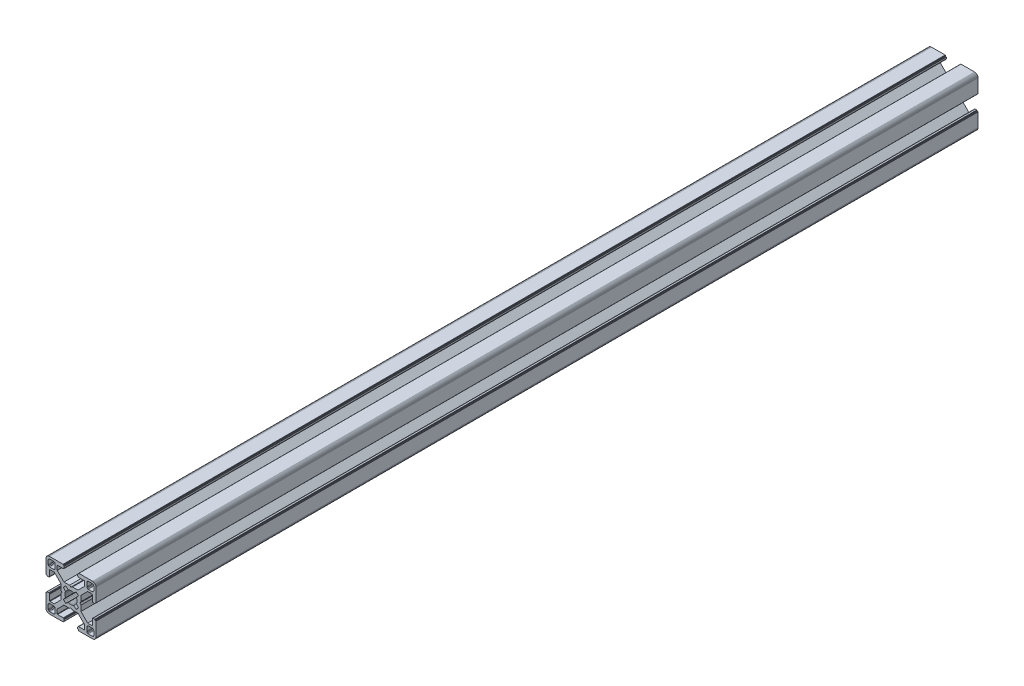
SolidWorks part; units mm, degrees
ref_plane "Front Plane" through (0, 0, 0) normal (0, 0, 1) x (1, 0, 0)
ref_plane "Top Plane" through (0, 0, 0) normal (0, 1, 0) x (1, 0, 0)
ref_plane "Right Plane" through (0, 0, 0) normal (1, 0, 0) x (0, 0, -1)
ref_plane "Plane1" through (0, 0, 0) normal (0, 0, 1) x (1, 0, 0)
sketch "Sketch1" plane through (0, 0, 0) normal (0, 0, 1) x (1, 0, 0)
  line L0 (28.3473, 29.9696) -> (28, 30)
  line L1 (28, 30) -> (19.75, 30)
  line L2 (19.75, 30) -> (19.7153, 29.997)
  line L3 (19.7153, 29.997) -> (19.6816, 29.9879)
  line L4 (19.6816, 29.9879) -> (19.65, 29.9732)
  line L5 (19.65, 29.9732) -> (19.6214, 29.9532)
  line L6 (19.6214, 29.9532) -> (19.5968, 29.9286)
  line L7 (19.5968, 29.9286) -> (19.5768, 29.9)
  line L8 (19.5768, 29.9) -> (19.5621, 29.8684)
  line L9 (19.5621, 29.8684) -> (19.553, 29.8347)
  line L10 (19.553, 29.8347) -> (19.55, 29.8)
  line L11 (19.55, 29.8) -> (19.55, 29.7)
  line L12 (19.55, 29.7) -> (19.547, 29.6653)
  line L13 (19.547, 29.6653) -> (19.5379, 29.6316)
  line L14 (19.5379, 29.6316) -> (19.5232, 29.6)
  line L15 (19.5232, 29.6) -> (19.5032, 29.5714)
  line L16 (19.5032, 29.5714) -> (19.4786, 29.5468)
  line L17 (19.4786, 29.5468) -> (19.45, 29.5268)
  line L18 (19.45, 29.5268) -> (19.4184, 29.5121)
  line L19 (19.4184, 29.5121) -> (19.3847, 29.503)
  line L20 (19.3847, 29.503) -> (19.35, 29.5)
  line L21 (19.35, 29.5) -> (19.25, 29.5)
  line L22 (19.25, 29.5) -> (19.2153, 29.497)
  line L23 (19.2153, 29.497) -> (19.1816, 29.4879)
  line L24 (19.1816, 29.4879) -> (19.15, 29.4732)
  line L25 (19.15, 29.4732) -> (19.1214, 29.4532)
  line L26 (19.1214, 29.4532) -> (19.0968, 29.4286)
  line L27 (19.0968, 29.4286) -> (19.0768, 29.4)
  line L28 (19.0768, 29.4) -> (19.0621, 29.3684)
  line L29 (19.0621, 29.3684) -> (19.053, 29.3347)
  line L30 (19.053, 29.3347) -> (19.05, 29.3)
  line L31 (19.05, 29.3) -> (19.05, 28.4)
  line L32 (19.05, 28.4) -> (19.0591, 28.2958)
  line L33 (19.0591, 28.2958) -> (19.0862, 28.1948)
  line L34 (19.0862, 28.1948) -> (19.1304, 28.1)
  line L35 (19.1304, 28.1) -> (19.1904, 28.0143)
  line L36 (19.1904, 28.0143) -> (19.2643, 27.9404)
  line L37 (19.2643, 27.9404) -> (19.35, 27.8804)
  line L38 (19.35, 27.8804) -> (19.4448, 27.8362)
  line L39 (19.4448, 27.8362) -> (19.5458, 27.8091)
  line L40 (19.5458, 27.8091) -> (19.65, 27.8)
  line L41 (19.65, 27.8) -> (23.05, 27.8)
  line L42 (23.05, 27.8) -> (23.0847, 27.7969)
  line L43 (23.0847, 27.7969) -> (23.1184, 27.7879)
  line L44 (23.1184, 27.7879) -> (23.15, 27.7732)
  line L45 (23.15, 27.7732) -> (23.1786, 27.7532)
  line L46 (23.1786, 27.7532) -> (23.2032, 27.7285)
  line L47 (23.2032, 27.7285) -> (23.2232, 27.7)
  line L48 (23.2232, 27.7) -> (23.2379, 27.6684)
  line L49 (23.2379, 27.6684) -> (23.247, 27.6347)
  line L50 (23.247, 27.6347) -> (23.25, 27.6)
  line L51 (23.25, 27.6) -> (23.25, 25.05)
  line L52 (23.25, 25.05) -> (19.2045, 21)
  line L53 (19.2045, 21) -> (15.9, 21)
  line L54 (15.9, 21) -> (15, 20.4848)
  line L55 (15, 20.4848) -> (14.1, 21)
  line L56 (14.1, 21) -> (10.7955, 21)
  line L57 (10.7955, 21) -> (7.9973, 23.8013)
  line L58 (7.9973, 23.8013) -> (6.75, 25.05)
  line L59 (6.75, 25.05) -> (6.75, 27.6)
  line L60 (6.75, 27.6) -> (6.753, 27.6347)
  line L61 (6.753, 27.6347) -> (6.7621, 27.6684)
  line L62 (6.7621, 27.6684) -> (6.7768, 27.7)
  line L63 (6.7768, 27.7) -> (6.7968, 27.7285)
  line L64 (6.7968, 27.7285) -> (6.8215, 27.7532)
  line L65 (6.8215, 27.7532) -> (6.85, 27.7732)
  line L66 (6.85, 27.7732) -> (6.8816, 27.7879)
  line L67 (6.8816, 27.7879) -> (6.9153, 27.7969)
  line L68 (6.9153, 27.7969) -> (6.95, 27.8)
  line L69 (6.95, 27.8) -> (10.35, 27.8)
  line L70 (10.35, 27.8) -> (10.4542, 27.8091)
  line L71 (10.4542, 27.8091) -> (10.5552, 27.8362)
  line L72 (10.5552, 27.8362) -> (10.65, 27.8804)
  line L73 (10.65, 27.8804) -> (10.7357, 27.9404)
  line L74 (10.7357, 27.9404) -> (10.8096, 28.0143)
  line L75 (10.8096, 28.0143) -> (10.8696, 28.1)
  line L76 (10.8696, 28.1) -> (10.9138, 28.1948)
  line L77 (10.9138, 28.1948) -> (10.9409, 28.2958)
  line L78 (10.9409, 28.2958) -> (10.95, 28.4)
  line L79 (10.95, 28.4) -> (10.95, 29.3)
  line L80 (10.95, 29.3) -> (10.947, 29.3347)
  line L81 (10.947, 29.3347) -> (10.938, 29.3684)
  line L82 (10.938, 29.3684) -> (10.9232, 29.4)
  line L83 (10.9232, 29.4) -> (10.9032, 29.4286)
  line L84 (10.9032, 29.4286) -> (10.8786, 29.4532)
  line L85 (10.8786, 29.4532) -> (10.85, 29.4732)
  line L86 (10.85, 29.4732) -> (10.8184, 29.4879)
  line L87 (10.8184, 29.4879) -> (10.7847, 29.497)
  line L88 (10.7847, 29.497) -> (10.75, 29.5)
  line L89 (10.75, 29.5) -> (10.65, 29.5)
  line L90 (10.65, 29.5) -> (10.6153, 29.503)
  line L91 (10.6153, 29.503) -> (10.5816, 29.5121)
  line L92 (10.5816, 29.5121) -> (10.55, 29.5268)
  line L93 (10.55, 29.5268) -> (10.5214, 29.5468)
  line L94 (10.5214, 29.5468) -> (10.4968, 29.5714)
  line L95 (10.4968, 29.5714) -> (10.4768, 29.6)
  line L96 (10.4768, 29.6) -> (10.4621, 29.6316)
  line L97 (10.4621, 29.6316) -> (10.453, 29.6653)
  line L98 (10.453, 29.6653) -> (10.45, 29.7)
  line L99 (10.45, 29.7) -> (10.45, 29.8)
  line L100 (10.45, 29.8) -> (10.447, 29.8347)
  line L101 (10.447, 29.8347) -> (10.4379, 29.8684)
  line L102 (10.4379, 29.8684) -> (10.4232, 29.9)
  line L103 (10.4232, 29.9) -> (10.4032, 29.9286)
  line L104 (10.4032, 29.9286) -> (10.3786, 29.9532)
  line L105 (10.3786, 29.9532) -> (10.35, 29.9732)
  line L106 (10.35, 29.9732) -> (10.3184, 29.9879)
  line L107 (10.3184, 29.9879) -> (10.2847, 29.997)
  line L108 (10.2847, 29.997) -> (10.25, 30)
  line L109 (10.25, 30) -> (2, 30)
  line L110 (2, 30) -> (1.6527, 29.9696)
  line L111 (1.6527, 29.9696) -> (1.316, 29.8794)
  line L112 (1.316, 29.8794) -> (1, 29.7321)
  line L113 (1, 29.7321) -> (0.7144, 29.5321)
  line L114 (0.7144, 29.5321) -> (0.4679, 29.2856)
  line L115 (0.4679, 29.2856) -> (0.2679, 29)
  line L116 (0.2679, 29) -> (0.1206, 28.684)
  line L117 (0.1206, 28.684) -> (0.0304, 28.3473)
  line L118 (0.0304, 28.3473) -> (0, 28)
  line L119 (0, 28) -> (0, 19.75)
  line L120 (0, 19.75) -> (0.003, 19.7153)
  line L121 (0.003, 19.7153) -> (0.0121, 19.6816)
  line L122 (0.0121, 19.6816) -> (0.0268, 19.65)
  line L123 (0.0268, 19.65) -> (0.0468, 19.6214)
  line L124 (0.0468, 19.6214) -> (0.0714, 19.5968)
  line L125 (0.0714, 19.5968) -> (0.1, 19.5768)
  line L126 (0.1, 19.5768) -> (0.1316, 19.5621)
  line L127 (0.1316, 19.5621) -> (0.1653, 19.553)
  line L128 (0.1653, 19.553) -> (0.2, 19.55)
  line L129 (0.2, 19.55) -> (0.3, 19.55)
  line L130 (0.3, 19.55) -> (0.3347, 19.547)
  line L131 (0.3347, 19.547) -> (0.3684, 19.5379)
  line L132 (0.3684, 19.5379) -> (0.4, 19.5232)
  line L133 (0.4, 19.5232) -> (0.4286, 19.5032)
  line L134 (0.4286, 19.5032) -> (0.4532, 19.4786)
  line L135 (0.4532, 19.4786) -> (0.4732, 19.45)
  line L136 (0.4732, 19.45) -> (0.4879, 19.4184)
  line L137 (0.4879, 19.4184) -> (0.497, 19.3847)
  line L138 (0.497, 19.3847) -> (0.5, 19.35)
  line L139 (0.5, 19.35) -> (0.5, 19.25)
  line L140 (0.5, 19.25) -> (0.503, 19.2153)
  line L141 (0.503, 19.2153) -> (0.5121, 19.1816)
  line L142 (0.5121, 19.1816) -> (0.5268, 19.15)
  line L143 (0.5268, 19.15) -> (0.5468, 19.1214)
  line L144 (0.5468, 19.1214) -> (0.5714, 19.0968)
  line L145 (0.5714, 19.0968) -> (0.6, 19.0768)
  line L146 (0.6, 19.0768) -> (0.6316, 19.0621)
  line L147 (0.6316, 19.0621) -> (0.6653, 19.053)
  line L148 (0.6653, 19.053) -> (0.7, 19.05)
  line L149 (0.7, 19.05) -> (1.6, 19.05)
  line L150 (1.6, 19.05) -> (1.7042, 19.0591)
  line L151 (1.7042, 19.0591) -> (1.8052, 19.0862)
  line L152 (1.8052, 19.0862) -> (1.9, 19.1304)
  line L153 (1.9, 19.1304) -> (1.9857, 19.1904)
  line L154 (1.9857, 19.1904) -> (2.0596, 19.2643)
  line L155 (2.0596, 19.2643) -> (2.1196, 19.35)
  line L156 (2.1196, 19.35) -> (2.1638, 19.4448)
  line L157 (2.1638, 19.4448) -> (2.1909, 19.5458)
  line L158 (2.1909, 19.5458) -> (2.2, 19.65)
  line L159 (2.2, 19.65) -> (2.2, 23.05)
  line L160 (2.2, 23.05) -> (2.203, 23.0847)
  line L161 (2.203, 23.0847) -> (2.2121, 23.1184)
  line L162 (2.2121, 23.1184) -> (2.2268, 23.15)
  line L163 (2.2268, 23.15) -> (2.2468, 23.1786)
  line L164 (2.2468, 23.1786) -> (2.2714, 23.2032)
  line L165 (2.2714, 23.2032) -> (2.3, 23.2232)
  line L166 (2.3, 23.2232) -> (2.3316, 23.2379)
  line L167 (2.3316, 23.2379) -> (2.3653, 23.247)
  line L168 (2.3653, 23.247) -> (2.4, 23.25)
  line L169 (2.4, 23.25) -> (4.95, 23.25)
  line L170 (4.95, 23.25) -> (7.9973, 20.2027)
  line L171 (7.9973, 20.2027) -> (8.9955, 19.2045)
  line L172 (8.9955, 19.2045) -> (8.9955, 15.9)
  line L173 (8.9955, 15.9) -> (9.5151, 15)
  line L174 (9.5151, 15) -> (8.9955, 14.1)
  line L175 (8.9955, 14.1) -> (8.9955, 10.7955)
  line L176 (8.9955, 10.7955) -> (4.95, 6.75)
  line L177 (4.95, 6.75) -> (2.4, 6.75)
  line L178 (2.4, 6.75) -> (2.3653, 6.753)
  line L179 (2.3653, 6.753) -> (2.3316, 6.7621)
  line L180 (2.3316, 6.7621) -> (2.3, 6.7768)
  line L181 (2.3, 6.7768) -> (2.2714, 6.7968)
  line L182 (2.2714, 6.7968) -> (2.2468, 6.8214)
  line L183 (2.2468, 6.8214) -> (2.2268, 6.85)
  line L184 (2.2268, 6.85) -> (2.2121, 6.8816)
  line L185 (2.2121, 6.8816) -> (2.203, 6.9153)
  line L186 (2.203, 6.9153) -> (2.2, 6.95)
  line L187 (2.2, 6.95) -> (2.2, 10.35)
  line L188 (2.2, 10.35) -> (2.1909, 10.4542)
  line L189 (2.1909, 10.4542) -> (2.1638, 10.5552)
  line L190 (2.1638, 10.5552) -> (2.1196, 10.65)
  line L191 (2.1196, 10.65) -> (2.0596, 10.7357)
  line L192 (2.0596, 10.7357) -> (1.9857, 10.8096)
  line L193 (1.9857, 10.8096) -> (1.9, 10.8696)
  line L194 (1.9, 10.8696) -> (1.8052, 10.9138)
  line L195 (1.8052, 10.9138) -> (1.7042, 10.9409)
  line L196 (1.7042, 10.9409) -> (1.6, 10.95)
  line L197 (1.6, 10.95) -> (0.7, 10.95)
  line L198 (0.7, 10.95) -> (0.6653, 10.9469)
  line L199 (0.6653, 10.9469) -> (0.6316, 10.9379)
  line L200 (0.6316, 10.9379) -> (0.6, 10.9232)
  line L201 (0.6, 10.9232) -> (0.5715, 10.9032)
  line L202 (0.5715, 10.9032) -> (0.5468, 10.8785)
  line L203 (0.5468, 10.8785) -> (0.5268, 10.85)
  line L204 (0.5268, 10.85) -> (0.5121, 10.8184)
  line L205 (0.5121, 10.8184) -> (0.503, 10.7847)
  line L206 (0.503, 10.7847) -> (0.5, 10.75)
  line L207 (0.5, 10.75) -> (0.5, 10.65)
  line L208 (0.5, 10.65) -> (0.497, 10.6153)
  line L209 (0.497, 10.6153) -> (0.4879, 10.5816)
  line L210 (0.4879, 10.5816) -> (0.4732, 10.55)
  line L211 (0.4732, 10.55) -> (0.4532, 10.5214)
  line L212 (0.4532, 10.5214) -> (0.4286, 10.4968)
  line L213 (0.4286, 10.4968) -> (0.4, 10.4768)
  line L214 (0.4, 10.4768) -> (0.3684, 10.4621)
  line L215 (0.3684, 10.4621) -> (0.3347, 10.453)
  line L216 (0.3347, 10.453) -> (0.3, 10.45)
  line L217 (0.3, 10.45) -> (0.2, 10.45)
  line L218 (0.2, 10.45) -> (0.1653, 10.447)
  line L219 (0.1653, 10.447) -> (0.1316, 10.4379)
  line L220 (0.1316, 10.4379) -> (0.1, 10.4232)
  line L221 (0.1, 10.4232) -> (0.0714, 10.4032)
  line L222 (0.0714, 10.4032) -> (0.0468, 10.3786)
  line L223 (0.0468, 10.3786) -> (0.0268, 10.35)
  line L224 (0.0268, 10.35) -> (0.0121, 10.3184)
  line L225 (0.0121, 10.3184) -> (0.003, 10.2847)
  line L226 (0.003, 10.2847) -> (0, 10.25)
  line L227 (0, 10.25) -> (0, 2)
  line L228 (0, 2) -> (0.0304, 1.6527)
  line L229 (0.0304, 1.6527) -> (0.1206, 1.316)
  line L230 (0.1206, 1.316) -> (0.2679, 1)
  line L231 (0.2679, 1) -> (0.4679, 0.7144)
  line L232 (0.4679, 0.7144) -> (0.7144, 0.4679)
  line L233 (0.7144, 0.4679) -> (1, 0.2679)
  line L234 (1, 0.2679) -> (1.316, 0.1206)
  line L235 (1.316, 0.1206) -> (1.6527, 0.0304)
  line L236 (1.6527, 0.0304) -> (2, 0)
  line L237 (2, 0) -> (10.25, 0)
  line L238 (10.25, 0) -> (10.2847, 0.003)
  line L239 (10.2847, 0.003) -> (10.3184, 0.0121)
  line L240 (10.3184, 0.0121) -> (10.35, 0.0268)
  line L241 (10.35, 0.0268) -> (10.3786, 0.0468)
  line L242 (10.3786, 0.0468) -> (10.4032, 0.0714)
  line L243 (10.4032, 0.0714) -> (10.4232, 0.1)
  line L244 (10.4232, 0.1) -> (10.4379, 0.1316)
  line L245 (10.4379, 0.1316) -> (10.447, 0.1653)
  line L246 (10.447, 0.1653) -> (10.45, 0.2)
  line L247 (10.45, 0.2) -> (10.45, 0.3)
  line L248 (10.45, 0.3) -> (10.453, 0.3347)
  line L249 (10.453, 0.3347) -> (10.4621, 0.3684)
  line L250 (10.4621, 0.3684) -> (10.4768, 0.4)
  line L251 (10.4768, 0.4) -> (10.4968, 0.4286)
  line L252 (10.4968, 0.4286) -> (10.5214, 0.4532)
  line L253 (10.5214, 0.4532) -> (10.55, 0.4732)
  line L254 (10.55, 0.4732) -> (10.5816, 0.4879)
  line L255 (10.5816, 0.4879) -> (10.6153, 0.497)
  line L256 (10.6153, 0.497) -> (10.65, 0.5)
  line L257 (10.65, 0.5) -> (10.75, 0.5)
  line L258 (10.75, 0.5) -> (10.7847, 0.503)
  line L259 (10.7847, 0.503) -> (10.8184, 0.5121)
  line L260 (10.8184, 0.5121) -> (10.85, 0.5268)
  line L261 (10.85, 0.5268) -> (10.8785, 0.5468)
  line L262 (10.8785, 0.5468) -> (10.9032, 0.5715)
  line L263 (10.9032, 0.5715) -> (10.9232, 0.6)
  line L264 (10.9232, 0.6) -> (10.9379, 0.6316)
  line L265 (10.9379, 0.6316) -> (10.9469, 0.6653)
  line L266 (10.9469, 0.6653) -> (10.95, 0.7)
  line L267 (10.95, 0.7) -> (10.95, 1.6)
  line L268 (10.95, 1.6) -> (10.9409, 1.7042)
  line L269 (10.9409, 1.7042) -> (10.9138, 1.8052)
  line L270 (10.9138, 1.8052) -> (10.8696, 1.9)
  line L271 (10.8696, 1.9) -> (10.8096, 1.9857)
  line L272 (10.8096, 1.9857) -> (10.7357, 2.0596)
  line L273 (10.7357, 2.0596) -> (10.65, 2.1196)
  line L274 (10.65, 2.1196) -> (10.5552, 2.1638)
  line L275 (10.5552, 2.1638) -> (10.4542, 2.1909)
  line L276 (10.4542, 2.1909) -> (10.35, 2.2)
  line L277 (10.35, 2.2) -> (6.95, 2.2)
  line L278 (6.95, 2.2) -> (6.9153, 2.203)
  line L279 (6.9153, 2.203) -> (6.8816, 2.212)
  line L280 (6.8816, 2.212) -> (6.85, 2.2268)
  line L281 (6.85, 2.2268) -> (6.8215, 2.2468)
  line L282 (6.8215, 2.2468) -> (6.7968, 2.2714)
  line L283 (6.7968, 2.2714) -> (6.7768, 2.3)
  line L284 (6.7768, 2.3) -> (6.7621, 2.3316)
  line L285 (6.7621, 2.3316) -> (6.753, 2.3653)
  line L286 (6.753, 2.3653) -> (6.75, 2.4)
  line L287 (6.75, 2.4) -> (6.75, 4.95)
  line L288 (6.75, 4.95) -> (9.7875, 7.9908)
  line L289 (9.7875, 7.9908) -> (10.7955, 9)
  line L290 (10.7955, 9) -> (14.1, 9)
  line L291 (14.1, 9) -> (15, 9.5151)
  line L292 (15, 9.5151) -> (15.9, 9)
  line L293 (15.9, 9) -> (19.2045, 9)
  line L294 (19.2045, 9) -> (20.2126, 7.9908)
  line L295 (20.2126, 7.9908) -> (23.25, 4.95)
  line L296 (23.25, 4.95) -> (23.25, 2.4)
  line L297 (23.25, 2.4) -> (23.247, 2.3653)
  line L298 (23.247, 2.3653) -> (23.2379, 2.3316)
  line L299 (23.2379, 2.3316) -> (23.2232, 2.3)
  line L300 (23.2232, 2.3) -> (23.2032, 2.2714)
  line L301 (23.2032, 2.2714) -> (23.1786, 2.2468)
  line L302 (23.1786, 2.2468) -> (23.15, 2.2268)
  line L303 (23.15, 2.2268) -> (23.1184, 2.212)
  line L304 (23.1184, 2.212) -> (23.0847, 2.203)
  line L305 (23.0847, 2.203) -> (23.05, 2.2)
  line L306 (23.05, 2.2) -> (19.65, 2.2)
  line L307 (19.65, 2.2) -> (19.5458, 2.1909)
  line L308 (19.5458, 2.1909) -> (19.4448, 2.1638)
  line L309 (19.4448, 2.1638) -> (19.35, 2.1196)
  line L310 (19.35, 2.1196) -> (19.2643, 2.0596)
  line L311 (19.2643, 2.0596) -> (19.1904, 1.9857)
  line L312 (19.1904, 1.9857) -> (19.1304, 1.9)
  line L313 (19.1304, 1.9) -> (19.0862, 1.8052)
  line L314 (19.0862, 1.8052) -> (19.0591, 1.7042)
  line L315 (19.0591, 1.7042) -> (19.05, 1.6)
  line L316 (19.05, 1.6) -> (19.05, 0.7)
  line L317 (19.05, 0.7) -> (19.053, 0.6653)
  line L318 (19.053, 0.6653) -> (19.0621, 0.6316)
  line L319 (19.0621, 0.6316) -> (19.0768, 0.6)
  line L320 (19.0768, 0.6) -> (19.0968, 0.5714)
  line L321 (19.0968, 0.5714) -> (19.1214, 0.5468)
  line L322 (19.1214, 0.5468) -> (19.15, 0.5268)
  line L323 (19.15, 0.5268) -> (19.1816, 0.5121)
  line L324 (19.1816, 0.5121) -> (19.2153, 0.503)
  line L325 (19.2153, 0.503) -> (19.25, 0.5)
  line L326 (19.25, 0.5) -> (19.35, 0.5)
  line L327 (19.35, 0.5) -> (19.3847, 0.497)
  line L328 (19.3847, 0.497) -> (19.4184, 0.4879)
  line L329 (19.4184, 0.4879) -> (19.45, 0.4732)
  line L330 (19.45, 0.4732) -> (19.4786, 0.4532)
  line L331 (19.4786, 0.4532) -> (19.5032, 0.4286)
  line L332 (19.5032, 0.4286) -> (19.5232, 0.4)
  line L333 (19.5232, 0.4) -> (19.5379, 0.3684)
  line L334 (19.5379, 0.3684) -> (19.547, 0.3347)
  line L335 (19.547, 0.3347) -> (19.55, 0.3)
  line L336 (19.55, 0.3) -> (19.55, 0.2)
  line L337 (19.55, 0.2) -> (19.553, 0.1653)
  line L338 (19.553, 0.1653) -> (19.5621, 0.1316)
  line L339 (19.5621, 0.1316) -> (19.5768, 0.1)
  line L340 (19.5768, 0.1) -> (19.5968, 0.0714)
  line L341 (19.5968, 0.0714) -> (19.6214, 0.0468)
  line L342 (19.6214, 0.0468) -> (19.65, 0.0268)
  line L343 (19.65, 0.0268) -> (19.6816, 0.0121)
  line L344 (19.6816, 0.0121) -> (19.7153, 0.003)
  line L345 (19.7153, 0.003) -> (19.75, 0)
  line L346 (19.75, 0) -> (28, 0)
  line L347 (28, 0) -> (28.3473, 0.0304)
  line L348 (28.3473, 0.0304) -> (28.684, 0.1206)
  line L349 (28.684, 0.1206) -> (29, 0.2679)
  line L350 (29, 0.2679) -> (29.2856, 0.4679)
  line L351 (29.2856, 0.4679) -> (29.5321, 0.7144)
  line L352 (29.5321, 0.7144) -> (29.7321, 1)
  line L353 (29.7321, 1) -> (29.8794, 1.316)
  line L354 (29.8794, 1.316) -> (29.9696, 1.6527)
  line L355 (29.9696, 1.6527) -> (30, 2)
  line L356 (30, 2) -> (30, 10.25)
  line L357 (30, 10.25) -> (29.997, 10.2847)
  line L358 (29.997, 10.2847) -> (29.988, 10.3184)
  line L359 (29.988, 10.3184) -> (29.9732, 10.35)
  line L360 (29.9732, 10.35) -> (29.9532, 10.3785)
  line L361 (29.9532, 10.3785) -> (29.9286, 10.4032)
  line L362 (29.9286, 10.4032) -> (29.9, 10.4232)
  line L363 (29.9, 10.4232) -> (29.8684, 10.4379)
  line L364 (29.8684, 10.4379) -> (29.8347, 10.447)
  line L365 (29.8347, 10.447) -> (29.8, 10.45)
  line L366 (29.8, 10.45) -> (29.7, 10.45)
  line L367 (29.7, 10.45) -> (29.6649, 10.4534)
  line L368 (29.6649, 10.4534) -> (29.6312, 10.4624)
  line L369 (29.6312, 10.4624) -> (29.5996, 10.4772)
  line L370 (29.5996, 10.4772) -> (29.5711, 10.4972)
  line L371 (29.5711, 10.4972) -> (29.5464, 10.5218)
  line L372 (29.5464, 10.5218) -> (29.5264, 10.5504)
  line L373 (29.5264, 10.5504) -> (29.5117, 10.582)
  line L374 (29.5117, 10.582) -> (29.5027, 10.6156)
  line L375 (29.5027, 10.6156) -> (29.4996, 10.6504)
  line L376 (29.4996, 10.6504) -> (29.4996, 10.7504)
  line L377 (29.4996, 10.7504) -> (29.497, 10.7847)
  line L378 (29.497, 10.7847) -> (29.4879, 10.8184)
  line L379 (29.4879, 10.8184) -> (29.4732, 10.85)
  line L380 (29.4732, 10.85) -> (29.4532, 10.8785)
  line L381 (29.4532, 10.8785) -> (29.4286, 10.9032)
  line L382 (29.4286, 10.9032) -> (29.4, 10.9232)
  line L383 (29.4, 10.9232) -> (29.3684, 10.9379)
  line L384 (29.3684, 10.9379) -> (29.3347, 10.9469)
  line L385 (29.3347, 10.9469) -> (29.3, 10.95)
  line L386 (29.3, 10.95) -> (28.4, 10.95)
  line L387 (28.4, 10.95) -> (28.2958, 10.9409)
  line L388 (28.2958, 10.9409) -> (28.1948, 10.9138)
  line L389 (28.1948, 10.9138) -> (28.1, 10.8696)
  line L390 (28.1, 10.8696) -> (28.0143, 10.8096)
  line L391 (28.0143, 10.8096) -> (27.9404, 10.7357)
  line L392 (27.9404, 10.7357) -> (27.8804, 10.65)
  line L393 (27.8804, 10.65) -> (27.8362, 10.5552)
  line L394 (27.8362, 10.5552) -> (27.8091, 10.4542)
  line L395 (27.8091, 10.4542) -> (27.8, 10.35)
  line L396 (27.8, 10.35) -> (27.8, 6.95)
  line L397 (27.8, 6.95) -> (27.797, 6.9153)
  line L398 (27.797, 6.9153) -> (27.7879, 6.8816)
  line L399 (27.7879, 6.8816) -> (27.7732, 6.85)
  line L400 (27.7732, 6.85) -> (27.7532, 6.8214)
  line L401 (27.7532, 6.8214) -> (27.7286, 6.7968)
  line L402 (27.7286, 6.7968) -> (27.7, 6.7768)
  line L403 (27.7, 6.7768) -> (27.6684, 6.7621)
  line L404 (27.6684, 6.7621) -> (27.6347, 6.753)
  line L405 (27.6347, 6.753) -> (27.6, 6.75)
  line L406 (27.6, 6.75) -> (25.05, 6.75)
  line L407 (25.05, 6.75) -> (23.8092, 7.9908)
  line L408 (23.8092, 7.9908) -> (21.0045, 10.7955)
  line L409 (21.0045, 10.7955) -> (21.0045, 14.1)
  line L410 (21.0045, 14.1) -> (20.4849, 15)
  line L411 (20.4849, 15) -> (21.0045, 15.9)
  line L412 (21.0045, 15.9) -> (21.0045, 19.2045)
  line L413 (21.0045, 19.2045) -> (25.05, 23.25)
  line L414 (25.05, 23.25) -> (27.6, 23.25)
  line L415 (27.6, 23.25) -> (27.6347, 23.247)
  line L416 (27.6347, 23.247) -> (27.6684, 23.2379)
  line L417 (27.6684, 23.2379) -> (27.7, 23.2232)
  line L418 (27.7, 23.2232) -> (27.7286, 23.2032)
  line L419 (27.7286, 23.2032) -> (27.7532, 23.1786)
  line L420 (27.7532, 23.1786) -> (27.7732, 23.15)
  line L421 (27.7732, 23.15) -> (27.7879, 23.1184)
  line L422 (27.7879, 23.1184) -> (27.797, 23.0847)
  line L423 (27.797, 23.0847) -> (27.8, 23.05)
  line L424 (27.8, 23.05) -> (27.8, 19.65)
  line L425 (27.8, 19.65) -> (27.8091, 19.5458)
  line L426 (27.8091, 19.5458) -> (27.8362, 19.4448)
  line L427 (27.8362, 19.4448) -> (27.8804, 19.35)
  line L428 (27.8804, 19.35) -> (27.9404, 19.2643)
  line L429 (27.9404, 19.2643) -> (28.0143, 19.1904)
  line L430 (28.0143, 19.1904) -> (28.1, 19.1304)
  line L431 (28.1, 19.1304) -> (28.1948, 19.0862)
  line L432 (28.1948, 19.0862) -> (28.2958, 19.0591)
  line L433 (28.2958, 19.0591) -> (28.4, 19.05)
  line L434 (28.4, 19.05) -> (29.3, 19.05)
  line L435 (29.3, 19.05) -> (29.3347, 19.053)
  line L436 (29.3347, 19.053) -> (29.3684, 19.0621)
  line L437 (29.3684, 19.0621) -> (29.4, 19.0768)
  line L438 (29.4, 19.0768) -> (29.4282, 19.0971)
  line L439 (29.4282, 19.0971) -> (29.4528, 19.1218)
  line L440 (29.4528, 19.1218) -> (29.4728, 19.1504)
  line L441 (29.4728, 19.1504) -> (29.4876, 19.182)
  line L442 (29.4876, 19.182) -> (29.4966, 19.2156)
  line L443 (29.4966, 19.2156) -> (29.4996, 19.2504)
  line L444 (29.4996, 19.2504) -> (29.4996, 19.3504)
  line L445 (29.4996, 19.3504) -> (29.5027, 19.3851)
  line L446 (29.5027, 19.3851) -> (29.5117, 19.4188)
  line L447 (29.5117, 19.4188) -> (29.5264, 19.4504)
  line L448 (29.5264, 19.4504) -> (29.5464, 19.4789)
  line L449 (29.5464, 19.4789) -> (29.5711, 19.5036)
  line L450 (29.5711, 19.5036) -> (29.5996, 19.5236)
  line L451 (29.5996, 19.5236) -> (29.6312, 19.5383)
  line L452 (29.6312, 19.5383) -> (29.6649, 19.5473)
  line L453 (29.6649, 19.5473) -> (29.7, 19.55)
  line L454 (29.7, 19.55) -> (29.8, 19.55)
  line L455 (29.8, 19.55) -> (29.8347, 19.553)
  line L456 (29.8347, 19.553) -> (29.8684, 19.5621)
  line L457 (29.8684, 19.5621) -> (29.9, 19.5768)
  line L458 (29.9, 19.5768) -> (29.9286, 19.5968)
  line L459 (29.9286, 19.5968) -> (29.9532, 19.6214)
  line L460 (29.9532, 19.6214) -> (29.9732, 19.65)
  line L461 (29.9732, 19.65) -> (29.9879, 19.6816)
  line L462 (29.9879, 19.6816) -> (29.997, 19.7153)
  line L463 (29.997, 19.7153) -> (30, 19.75)
  line L464 (30, 19.75) -> (30, 28)
  line L465 (30, 28) -> (29.9696, 28.3473)
  line L466 (29.9696, 28.3473) -> (29.8794, 28.684)
  line L467 (29.8794, 28.684) -> (29.7321, 29)
  line L468 (29.7321, 29) -> (29.5321, 29.2856)
  line L469 (29.5321, 29.2856) -> (29.2856, 29.5321)
  line L470 (29.2856, 29.5321) -> (29, 29.7321)
  line L471 (29, 29.7321) -> (28.684, 29.8794)
  line L472 (28.684, 29.8794) -> (28.3473, 29.9696)
  line L473 (1.3, 25.5) -> (1.3, 27.7)
  line L474 (1.3, 27.7) -> (1.3123, 27.8564)
  line L475 (1.3123, 27.8564) -> (1.3489, 28.009)
  line L476 (1.3489, 28.009) -> (1.409, 28.154)
  line L477 (1.409, 28.154) -> (1.491, 28.2878)
  line L478 (1.491, 28.2878) -> (1.5929, 28.4071)
  line L479 (1.5929, 28.4071) -> (1.7122, 28.509)
  line L480 (1.7122, 28.509) -> (1.846, 28.591)
  line L481 (1.846, 28.591) -> (1.991, 28.6511)
  line L482 (1.991, 28.6511) -> (2.1436, 28.6877)
  line L483 (2.1436, 28.6877) -> (2.3, 28.7)
  line L484 (2.3, 28.7) -> (4.5, 28.7)
  line L485 (4.5, 28.7) -> (4.6564, 28.6877)
  line L486 (4.6564, 28.6877) -> (4.809, 28.6511)
  line L487 (4.809, 28.6511) -> (4.954, 28.591)
  line L488 (4.954, 28.591) -> (5.0878, 28.509)
  line L489 (5.0878, 28.509) -> (5.2071, 28.4071)
  line L490 (5.2071, 28.4071) -> (5.309, 28.2878)
  line L491 (5.309, 28.2878) -> (5.391, 28.154)
  line L492 (5.391, 28.154) -> (5.4511, 28.009)
  line L493 (5.4511, 28.009) -> (5.4877, 27.8564)
  line L494 (5.4877, 27.8564) -> (5.5, 27.7)
  line L495 (5.5, 27.7) -> (5.5, 25.5)
  line L496 (5.5, 25.5) -> (5.4877, 25.3436)
  line L497 (5.4877, 25.3436) -> (5.4511, 25.191)
  line L498 (5.4511, 25.191) -> (5.391, 25.046)
  line L499 (5.391, 25.046) -> (5.309, 24.9122)
  line L500 (5.309, 24.9122) -> (5.2071, 24.7929)
  line L501 (5.2071, 24.7929) -> (5.0878, 24.691)
  line L502 (5.0878, 24.691) -> (4.954, 24.609)
  line L503 (4.954, 24.609) -> (4.809, 24.5489)
  line L504 (4.809, 24.5489) -> (4.6564, 24.5123)
  line L505 (4.6564, 24.5123) -> (4.5, 24.5)
  line L506 (4.5, 24.5) -> (2.3, 24.5)
  line L507 (2.3, 24.5) -> (2.1436, 24.5123)
  line L508 (2.1436, 24.5123) -> (1.991, 24.5489)
  line L509 (1.991, 24.5489) -> (1.846, 24.609)
  line L510 (1.846, 24.609) -> (1.7122, 24.691)
  line L511 (1.7122, 24.691) -> (1.5929, 24.7929)
  line L512 (1.5929, 24.7929) -> (1.491, 24.9122)
  line L513 (1.491, 24.9122) -> (1.409, 25.046)
  line L514 (1.409, 25.046) -> (1.3489, 25.191)
  line L515 (1.3489, 25.191) -> (1.3123, 25.3436)
  line L516 (1.3123, 25.3436) -> (1.3, 25.5)
  line L517 (25.3436, 28.6877) -> (25.5, 28.7)
  line L518 (25.5, 28.7) -> (27.7, 28.7)
  line L519 (27.7, 28.7) -> (27.8564, 28.6877)
  line L520 (27.8564, 28.6877) -> (28.009, 28.6511)
  line L521 (28.009, 28.6511) -> (28.154, 28.591)
  line L522 (28.154, 28.591) -> (28.2878, 28.509)
  line L523 (28.2878, 28.509) -> (28.4071, 28.4071)
  line L524 (28.4071, 28.4071) -> (28.509, 28.2878)
  line L525 (28.509, 28.2878) -> (28.591, 28.154)
  line L526 (28.591, 28.154) -> (28.6511, 28.009)
  line L527 (28.6511, 28.009) -> (28.6877, 27.8564)
  line L528 (28.6877, 27.8564) -> (28.7, 27.7)
  line L529 (28.7, 27.7) -> (28.7, 25.5)
  line L530 (28.7, 25.5) -> (28.6877, 25.3436)
  line L531 (28.6877, 25.3436) -> (28.6511, 25.191)
  line L532 (28.6511, 25.191) -> (28.591, 25.046)
  line L533 (28.591, 25.046) -> (28.509, 24.9122)
  line L534 (28.509, 24.9122) -> (28.4071, 24.7929)
  line L535 (28.4071, 24.7929) -> (28.2878, 24.691)
  line L536 (28.2878, 24.691) -> (28.154, 24.609)
  line L537 (28.154, 24.609) -> (28.009, 24.5489)
  line L538 (28.009, 24.5489) -> (27.8564, 24.5123)
  line L539 (27.8564, 24.5123) -> (27.7, 24.5)
  line L540 (27.7, 24.5) -> (25.5, 24.5)
  line L541 (25.5, 24.5) -> (25.3436, 24.5123)
  line L542 (25.3436, 24.5123) -> (25.191, 24.5489)
  line L543 (25.191, 24.5489) -> (25.046, 24.609)
  line L544 (25.046, 24.609) -> (24.9122, 24.691)
  line L545 (24.9122, 24.691) -> (24.7929, 24.7929)
  line L546 (24.7929, 24.7929) -> (24.691, 24.9122)
  line L547 (24.691, 24.9122) -> (24.609, 25.046)
  line L548 (24.609, 25.046) -> (24.5489, 25.191)
  line L549 (24.5489, 25.191) -> (24.5123, 25.3436)
  line L550 (24.5123, 25.3436) -> (24.5, 25.5)
  line L551 (24.5, 25.5) -> (24.5, 27.7)
  line L552 (24.5, 27.7) -> (24.5123, 27.8564)
  line L553 (24.5123, 27.8564) -> (24.5489, 28.009)
  line L554 (24.5489, 28.009) -> (24.609, 28.154)
  line L555 (24.609, 28.154) -> (24.691, 28.2878)
  line L556 (24.691, 28.2878) -> (24.7929, 28.4071)
  line L557 (24.7929, 28.4071) -> (24.9122, 28.509)
  line L558 (24.9122, 28.509) -> (25.046, 28.591)
  line L559 (25.046, 28.591) -> (25.191, 28.6511)
  line L560 (25.191, 28.6511) -> (25.3436, 28.6877)
  line L561 (15, 18.65) -> (15.55, 18.6083)
  line L562 (15.55, 18.6083) -> (16.0875, 18.4842)
  line L563 (16.0875, 18.4842) -> (16.6001, 18.2806)
  line L564 (16.6001, 18.2806) -> (18.1359, 19.5184)
  line L565 (18.1359, 19.5184) -> (18.645, 19.1187)
  line L566 (18.645, 19.1187) -> (19.1036, 18.6621)
  line L567 (19.1036, 18.6621) -> (19.5053, 18.1547)
  line L568 (19.5053, 18.1547) -> (18.2806, 16.6001)
  line L569 (18.2806, 16.6001) -> (18.4842, 16.0875)
  line L570 (18.4842, 16.0875) -> (18.6083, 15.55)
  line L571 (18.6083, 15.55) -> (18.65, 15)
  line L572 (18.65, 15) -> (18.6083, 14.45)
  line L573 (18.6083, 14.45) -> (18.4842, 13.9125)
  line L574 (18.4842, 13.9125) -> (18.2806, 13.3999)
  line L575 (18.2806, 13.3999) -> (19.5053, 11.8453)
  line L576 (19.5053, 11.8453) -> (19.1036, 11.3379)
  line L577 (19.1036, 11.3379) -> (18.645, 10.8813)
  line L578 (18.645, 10.8813) -> (18.1359, 10.4816)
  line L579 (18.1359, 10.4816) -> (16.6001, 11.7194)
  line L580 (16.6001, 11.7194) -> (16.0875, 11.5158)
  line L581 (16.0875, 11.5158) -> (15.55, 11.3917)
  line L582 (15.55, 11.3917) -> (15, 11.35)
  line L583 (15, 11.35) -> (14.45, 11.3917)
  line L584 (14.45, 11.3917) -> (13.9125, 11.5158)
  line L585 (13.9125, 11.5158) -> (13.3999, 11.7194)
  line L586 (13.3999, 11.7194) -> (11.8641, 10.4816)
  line L587 (11.8641, 10.4816) -> (11.355, 10.8813)
  line L588 (11.355, 10.8813) -> (10.8964, 11.3379)
  line L589 (10.8964, 11.3379) -> (10.4947, 11.8453)
  line L590 (10.4947, 11.8453) -> (11.7194, 13.3999)
  line L591 (11.7194, 13.3999) -> (11.5158, 13.9125)
  line L592 (11.5158, 13.9125) -> (11.3917, 14.45)
  line L593 (11.3917, 14.45) -> (11.35, 15)
  line L594 (11.35, 15) -> (11.3917, 15.55)
  line L595 (11.3917, 15.55) -> (11.5158, 16.0875)
  line L596 (11.5158, 16.0875) -> (11.7194, 16.6001)
  line L597 (11.7194, 16.6001) -> (10.4947, 18.1547)
  line L598 (10.4947, 18.1547) -> (10.8964, 18.6621)
  line L599 (10.8964, 18.6621) -> (11.355, 19.1187)
  line L600 (11.355, 19.1187) -> (11.8641, 19.5184)
  line L601 (11.8641, 19.5184) -> (13.3999, 18.2806)
  line L602 (13.3999, 18.2806) -> (13.9125, 18.4842)
  line L603 (13.9125, 18.4842) -> (14.45, 18.6083)
  line L604 (14.45, 18.6083) -> (15, 18.65)
  line L605 (4.5, 1.3) -> (2.3, 1.3)
  line L606 (2.3, 1.3) -> (2.1436, 1.3123)
  line L607 (2.1436, 1.3123) -> (1.991, 1.3489)
  line L608 (1.991, 1.3489) -> (1.846, 1.409)
  line L609 (1.846, 1.409) -> (1.7122, 1.491)
  line L610 (1.7122, 1.491) -> (1.5929, 1.5929)
  line L611 (1.5929, 1.5929) -> (1.491, 1.7122)
  line L612 (1.491, 1.7122) -> (1.409, 1.846)
  line L613 (1.409, 1.846) -> (1.3489, 1.991)
  line L614 (1.3489, 1.991) -> (1.3123, 2.1436)
  line L615 (1.3123, 2.1436) -> (1.3, 2.3)
  line L616 (1.3, 2.3) -> (1.3, 4.5)
  line L617 (1.3, 4.5) -> (1.3123, 4.6564)
  line L618 (1.3123, 4.6564) -> (1.3489, 4.809)
  line L619 (1.3489, 4.809) -> (1.409, 4.954)
  line L620 (1.409, 4.954) -> (1.491, 5.0878)
  line L621 (1.491, 5.0878) -> (1.5929, 5.2071)
  line L622 (1.5929, 5.2071) -> (1.7122, 5.309)
  line L623 (1.7122, 5.309) -> (1.846, 5.391)
  line L624 (1.846, 5.391) -> (1.991, 5.4511)
  line L625 (1.991, 5.4511) -> (2.1436, 5.4877)
  line L626 (2.1436, 5.4877) -> (2.3, 5.5)
  line L627 (2.3, 5.5) -> (4.5, 5.5)
  line L628 (4.5, 5.5) -> (4.6564, 5.4877)
  line L629 (4.6564, 5.4877) -> (4.809, 5.4511)
  line L630 (4.809, 5.4511) -> (4.954, 5.391)
  line L631 (4.954, 5.391) -> (5.0878, 5.309)
  line L632 (5.0878, 5.309) -> (5.2071, 5.2071)
  line L633 (5.2071, 5.2071) -> (5.309, 5.0878)
  line L634 (5.309, 5.0878) -> (5.391, 4.954)
  line L635 (5.391, 4.954) -> (5.4511, 4.809)
  line L636 (5.4511, 4.809) -> (5.4877, 4.6564)
  line L637 (5.4877, 4.6564) -> (5.5, 4.5)
  line L638 (5.5, 4.5) -> (5.5, 2.3)
  line L639 (5.5, 2.3) -> (5.4877, 2.1436)
  line L640 (5.4877, 2.1436) -> (5.4511, 1.991)
  line L641 (5.4511, 1.991) -> (5.391, 1.846)
  line L642 (5.391, 1.846) -> (5.309, 1.7122)
  line L643 (5.309, 1.7122) -> (5.2071, 1.5929)
  line L644 (5.2071, 1.5929) -> (5.0878, 1.491)
  line L645 (5.0878, 1.491) -> (4.954, 1.409)
  line L646 (4.954, 1.409) -> (4.809, 1.3489)
  line L647 (4.809, 1.3489) -> (4.6564, 1.3123)
  line L648 (4.6564, 1.3123) -> (4.5, 1.3)
  line L649 (27.7, 1.3) -> (25.5, 1.3)
  line L650 (25.5, 1.3) -> (25.3436, 1.3123)
  line L651 (25.3436, 1.3123) -> (25.191, 1.3489)
  line L652 (25.191, 1.3489) -> (25.046, 1.409)
  line L653 (25.046, 1.409) -> (24.9122, 1.491)
  line L654 (24.9122, 1.491) -> (24.7929, 1.5929)
  line L655 (24.7929, 1.5929) -> (24.691, 1.7122)
  line L656 (24.691, 1.7122) -> (24.609, 1.846)
  line L657 (24.609, 1.846) -> (24.5489, 1.991)
  line L658 (24.5489, 1.991) -> (24.5123, 2.1436)
  line L659 (24.5123, 2.1436) -> (24.5, 2.3)
  line L660 (24.5, 2.3) -> (24.5, 4.5)
  line L661 (24.5, 4.5) -> (24.5123, 4.6564)
  line L662 (24.5123, 4.6564) -> (24.5489, 4.809)
  line L663 (24.5489, 4.809) -> (24.609, 4.954)
  line L664 (24.609, 4.954) -> (24.691, 5.0878)
  line L665 (24.691, 5.0878) -> (24.7929, 5.2071)
  line L666 (24.7929, 5.2071) -> (24.9122, 5.309)
  line L667 (24.9122, 5.309) -> (25.046, 5.391)
  line L668 (25.046, 5.391) -> (25.191, 5.4511)
  line L669 (25.191, 5.4511) -> (25.3436, 5.4877)
  line L670 (25.3436, 5.4877) -> (25.5, 5.5)
  line L671 (25.5, 5.5) -> (27.7, 5.5)
  line L672 (27.7, 5.5) -> (27.8564, 5.4877)
  line L673 (27.8564, 5.4877) -> (28.009, 5.4511)
  line L674 (28.009, 5.4511) -> (28.154, 5.391)
  line L675 (28.154, 5.391) -> (28.2878, 5.309)
  line L676 (28.2878, 5.309) -> (28.4071, 5.2071)
  line L677 (28.4071, 5.2071) -> (28.509, 5.0878)
  line L678 (28.509, 5.0878) -> (28.591, 4.954)
  line L679 (28.591, 4.954) -> (28.6511, 4.809)
  line L680 (28.6511, 4.809) -> (28.6877, 4.6564)
  line L681 (28.6877, 4.6564) -> (28.7, 4.5)
  line L682 (28.7, 4.5) -> (28.7, 2.3)
  line L683 (28.7, 2.3) -> (28.6877, 2.1436)
  line L684 (28.6877, 2.1436) -> (28.6511, 1.991)
  line L685 (28.6511, 1.991) -> (28.591, 1.846)
  line L686 (28.591, 1.846) -> (28.509, 1.7122)
  line L687 (28.509, 1.7122) -> (28.4071, 1.5929)
  line L688 (28.4071, 1.5929) -> (28.2878, 1.491)
  line L689 (28.2878, 1.491) -> (28.154, 1.409)
  line L690 (28.154, 1.409) -> (28.009, 1.3489)
  line L691 (28.009, 1.3489) -> (27.8564, 1.3123)
  line L692 (27.8564, 1.3123) -> (27.7, 1.3)
extrude "Boss-Extrude1" add sketch "Sketch1" against normal blind 530
